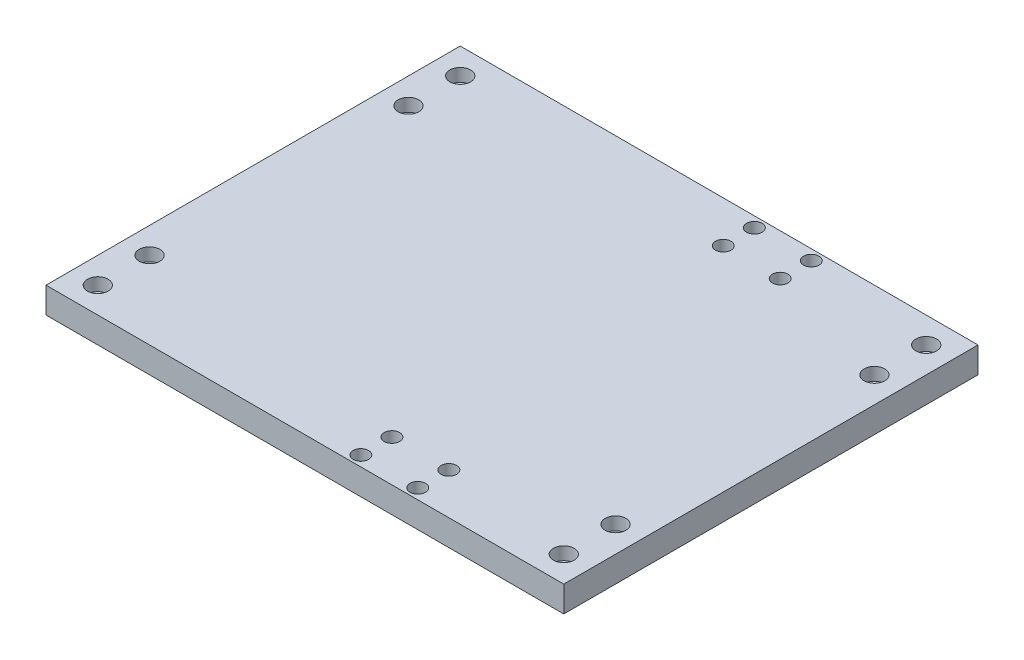
SolidWorks part; units mm, degrees
ref_plane "Front Plane" through (0, 0, 0) normal (0, 0, 1) x (1, 0, 0)
ref_plane "Top Plane" through (0, 0, 0) normal (0, 1, 0) x (1, 0, 0)
ref_plane "Right Plane" through (0, 0, 0) normal (1, 0, 0) x (0, 0, -1)
sketch "Sketch1" plane through (0, 0, 0) normal (0, 1, 0) x (1, 0, 0)
  line L0 (50, 80) -> (50, 0)
  line L1 (0, 0) -> (100, 0)
  line L2 (0, 0) -> (0, 80)
  line L3 (0, 80) -> (100, 80)
  line L4 (100, 0) -> (100, 80)
  line L5 (0, 40) -> (100, 40)
  circle A0 centre (95, 75) radius 1
  circle A1 centre (5, 75) radius 1
  circle A2 centre (5, 5) radius 1
  circle A3 centre (95, 5) radius 1
  circle A4 centre (95, 65) radius 1
  circle A5 centre (95, 15) radius 1
  circle A6 centre (5, 15) radius 1
  circle A7 centre (5, 65) radius 1
  dimension "D3" = 2
  dimension "D5" = 5
  dimension "D6" = 2
  dimension "D1" = 100
  dimension "D2" = 80
  dimension "D4" = 5
  dimension "D7" = 10
extrude "Boss-Extrude1" add sketch "Sketch1" along normal blind 5 contours L2 L5 L0 L3 A1 | L0 L5 L4 L3 A0 | L5 L0 L1 L4 A3 | L5 L2 L1 L0 A2
ref_plane "Plane1" through (0, 5, 0) normal (0, 1, 0) x (1, 0, 0)
sketch "Sketch2" plane through (0, 5, 0) normal (0, 1, 0) x (1, 0, 0)
  line L0 (50, 80) -> (50, 0)
  line L1 (0, 80) -> (100, 80) construction
  line L2 (-2.75, 0) -> (2.75, 0) construction
  line L3 (50, 40) -> (100, 40)
  line L4 (100, 0) -> (100, 80) construction
  line L5 (100, 40) -> (0, 40)
  line L6 (0, -2.75) -> (0, 2.75) construction
  circle A0 centre (5, 75) radius 2
  circle A1 centre (95, 75) radius 2
  circle A2 centre (95, 5) radius 2
  circle A3 centre (5, 5) radius 2
  circle A4 centre (5, 65) radius 2
  circle A5 centre (95, 65) radius 2
  circle A6 centre (95, 15) radius 2
  circle A7 centre (5, 15) radius 2
  dimension "D1" = 4
extrude "Cut-Extrude1" cut sketch "Sketch2" against normal blind 2.5 and the other way through all contours A3 | A0 | A1 | A2 | A4 | A7 | A6 | A5
ref_plane "Plane2" through (0, 5, 0) normal (0, 1, 0) x (1, 0, 0)
sketch "Sketch3" plane through (0, 5, 0) normal (0, 1, 0) x (1, 0, 0)
  line L0 (-2.75, 0) -> (2.75, 0) construction
  line L1 (56.8, 0) -> (71.8, 0)
  line L2 (56.8, 0) -> (56.8, 10)
  line L3 (56.8, 10) -> (71.8, 10)
  line L4 (71.8, 0) -> (71.8, 10)
  line L5 (0, -2.75) -> (0, 2.75) construction
  line L6 (64.3, 10) -> (64.3, 0)
  line L7 (64.3, 0) -> (56.8, 5)
  line L8 (56.8, 5) -> (71.8, 5)
  line L9 (50, 80) -> (50, 0)
  line L10 (0, 80) -> (100, 80) construction
  line L12 (100, 0) -> (100, 80) construction
  line L13 (100, 40) -> (0, 40)
  circle A0 centre (58.8, 8) radius 1
  circle A1 centre (69.8, 8) radius 1
  circle A2 centre (69.8, 2) radius 1
  circle A3 centre (58.8, 2) radius 1
  circle A4 centre (58.8, 72) radius 1
  circle A5 centre (58.8, 78) radius 1
  circle A6 centre (69.8, 78) radius 1
  circle A7 centre (69.8, 72) radius 1
  dimension "D4" = 2
  dimension "D6" = 2
  dimension "D1" = 56.8
  dimension "D2" = 15
  dimension "D3" = 10
  dimension "D5" = 2
extrude "Cut-Extrude2" cut sketch "Sketch3" against normal through all contours A0 | A1 | A3 | A2 | A5 | A7 | A6 | A4
ref_plane "Plane3" through (0, 5, 0) normal (0, 1, 0) x (1, 0, 0)
sketch "Sketch5" plane through (0, 5, 0) normal (0, 1, 0) x (1, 0, 0)
  circle A0 centre (58.8, 8) radius 1.5
  circle A1 centre (58.8, 2) radius 1.5
  circle A2 centre (69.8, 2) radius 1.5
  circle A3 centre (69.8, 8) radius 1.5
  circle A4 centre (58.8, 78) radius 1.5
  circle A5 centre (58.8, 72) radius 1.5
  circle A6 centre (69.8, 72) radius 1.5
  circle A7 centre (69.8, 78) radius 1.5
  dimension "D1" = 3
  dimension "D2" = 3
  dimension "D3" = 3
  dimension "D4" = 3
  dimension "D5" = 3
  dimension "D6" = 3
  dimension "D7" = 3
  dimension "D8" = 3
extrude "Cut-Extrude4" cut sketch "Sketch5" against normal blind 2.5
